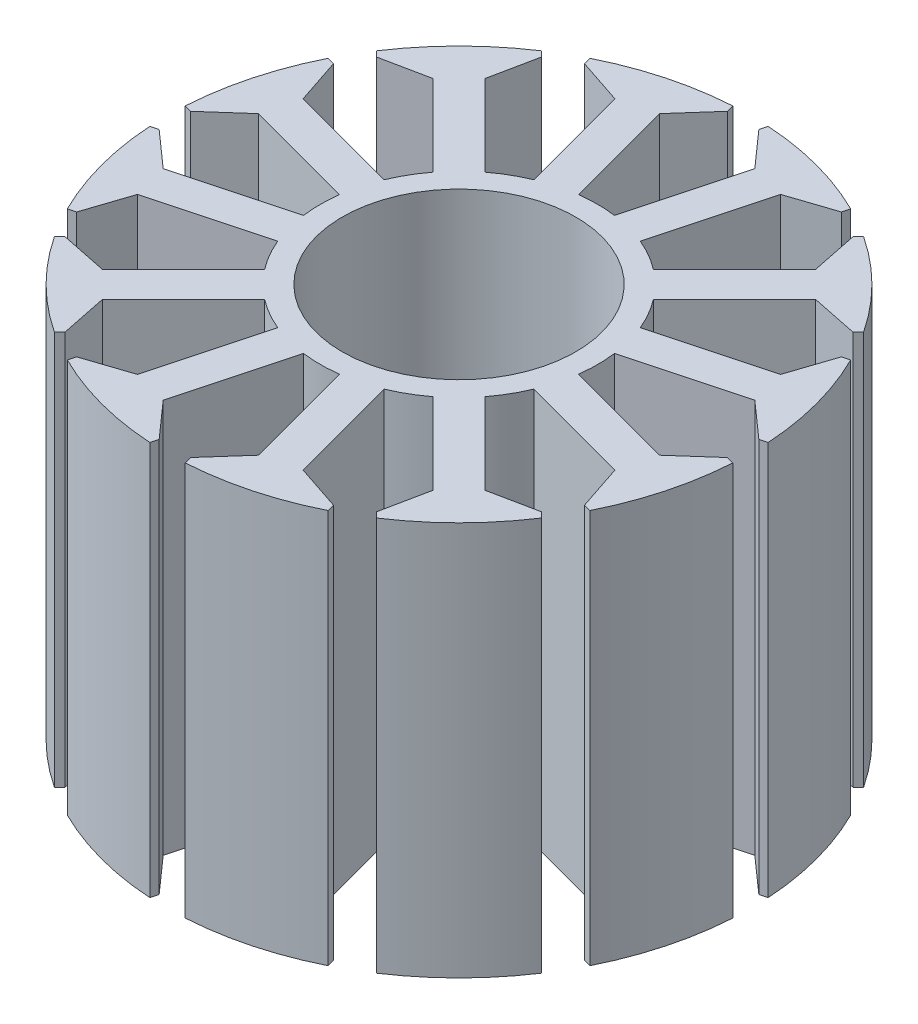
SolidWorks part; units mm, degrees
material "Ductile Iron"
ref_plane "Front Plane" through (0, 0, 0) normal (0, 0, 1) x (1, 0, 0)
ref_plane "Top Plane" through (0, 0, 0) normal (0, 1, 0) x (1, 0, 0)
ref_plane "Right Plane" through (0, 0, 0) normal (1, 0, 0) x (0, 0, -1)
sketch "Sketch1" plane through (0, 0, 0) normal (0, 1, 0) x (1, 0, 0)
  line L1 (0, 0) -> (0, 9.5) construction
  line L2 (0, 0) -> (10, 17.3205) construction
  line L3 (2.0706, 7.7274) -> (5.1764, 19.3185) construction
  line L4 (1.23, 9.42) -> (3.261, 17)
  line L5 (3.6448, 8.773) -> (5.6759, 16.353)
  line L6 (1.0755, 19.4634) -> (3.261, 17)
  line L7 (8.8003, 17.3935) -> (5.6759, 16.353)
  line L8 (16.3181, 10.6631) -> (13.0919, 11.3241)
  line L9 (8.8003, 17.3935) -> (8.9343, 17.8935)
  line L10 (1.0755, 19.4634) -> (1.2094, 19.9634)
  line L11 (16.3181, 10.6631) -> (16.6841, 11.0291)
  line L12 (10.6631, 16.3181) -> (11.0291, 16.6841)
  line L13 (10.6631, 16.3181) -> (11.3241, 13.0919)
  line L14 (5.7752, 7.543) -> (11.3241, 13.0919)
  line L15 (7.543, 5.7752) -> (13.0919, 11.3241)
  line L16 (19.4634, 1.0755) -> (17, 3.261)
  line L17 (19.4634, 1.0755) -> (19.9634, 1.2094)
  line L18 (17.3935, 8.8003) -> (17.8935, 8.9343)
  line L19 (17.3935, 8.8003) -> (16.353, 5.6759)
  line L20 (8.773, 3.6448) -> (16.353, 5.6759)
  line L21 (9.42, 1.23) -> (17, 3.261)
  line L22 (17.3935, -8.8003) -> (16.353, -5.6759)
  line L23 (17.3935, -8.8003) -> (17.8935, -8.9343)
  line L24 (19.4634, -1.0755) -> (19.9634, -1.2094)
  line L25 (19.4634, -1.0755) -> (17, -3.261)
  line L26 (9.42, -1.23) -> (17, -3.261)
  line L27 (8.773, -3.6448) -> (16.353, -5.6759)
  line L28 (10.6631, -16.3181) -> (11.3241, -13.0919)
  line L29 (10.6631, -16.3181) -> (11.0291, -16.6841)
  line L30 (16.3181, -10.6631) -> (16.6841, -11.0291)
  line L31 (16.3181, -10.6631) -> (13.0919, -11.3241)
  line L32 (7.543, -5.7752) -> (13.0919, -11.3241)
  line L33 (5.7752, -7.543) -> (11.3241, -13.0919)
  line L34 (1.0755, -19.4634) -> (3.261, -17)
  line L35 (1.0755, -19.4634) -> (1.2094, -19.9634)
  line L36 (8.8003, -17.3935) -> (8.9343, -17.8935)
  line L37 (8.8003, -17.3935) -> (5.6759, -16.353)
  line L38 (3.6448, -8.773) -> (5.6759, -16.353)
  line L39 (1.23, -9.42) -> (3.261, -17)
  line L40 (-8.8003, -17.3935) -> (-5.6759, -16.353)
  line L41 (-8.8003, -17.3935) -> (-8.9343, -17.8935)
  line L42 (-1.0755, -19.4634) -> (-1.2094, -19.9634)
  line L43 (-1.0755, -19.4634) -> (-3.261, -17)
  line L44 (-1.23, -9.42) -> (-3.261, -17)
  line L45 (-3.6448, -8.773) -> (-5.6759, -16.353)
  line L46 (-16.3181, -10.6631) -> (-13.0919, -11.3241)
  line L47 (-16.3181, -10.6631) -> (-16.6841, -11.0291)
  line L48 (-10.6631, -16.3181) -> (-11.0291, -16.6841)
  line L49 (-10.6631, -16.3181) -> (-11.3241, -13.0919)
  line L50 (-5.7752, -7.543) -> (-11.3241, -13.0919)
  line L51 (-7.543, -5.7752) -> (-13.0919, -11.3241)
  line L52 (-19.4634, -1.0755) -> (-17, -3.261)
  line L53 (-19.4634, -1.0755) -> (-19.9634, -1.2094)
  line L54 (-17.3935, -8.8003) -> (-17.8935, -8.9343)
  line L55 (-17.3935, -8.8003) -> (-16.353, -5.6759)
  line L56 (-8.773, -3.6448) -> (-16.353, -5.6759)
  line L57 (-9.42, -1.23) -> (-17, -3.261)
  line L58 (-17.3935, 8.8003) -> (-16.353, 5.6759)
  line L59 (-17.3935, 8.8003) -> (-17.8935, 8.9343)
  line L60 (-19.4634, 1.0755) -> (-19.9634, 1.2094)
  line L61 (-19.4634, 1.0755) -> (-17, 3.261)
  line L62 (-9.42, 1.23) -> (-17, 3.261)
  line L63 (-8.773, 3.6448) -> (-16.353, 5.6759)
  line L64 (-10.6631, 16.3181) -> (-11.3241, 13.0919)
  line L65 (-10.6631, 16.3181) -> (-11.0291, 16.6841)
  line L66 (-16.3181, 10.6631) -> (-16.6841, 11.0291)
  line L67 (-16.3181, 10.6631) -> (-13.0919, 11.3241)
  line L68 (-7.543, 5.7752) -> (-13.0919, 11.3241)
  line L69 (-5.7752, 7.543) -> (-11.3241, 13.0919)
  line L70 (-1.0755, 19.4634) -> (-3.261, 17)
  line L71 (-1.0755, 19.4634) -> (-1.2094, 19.9634)
  line L72 (-8.8003, 17.3935) -> (-8.9343, 17.8935)
  line L73 (-8.8003, 17.3935) -> (-5.6759, 16.353)
  line L74 (-3.6448, 8.773) -> (-5.6759, 16.353)
  line L75 (-1.23, 9.42) -> (-3.261, 17)
  arc A0 (8.9343, 17.8935) -> (1.2094, 19.9634) centre (0, 0) ccw
  arc A1 (4, 6.9282) -> (0, 8) centre (0, 0) ccw
  arc A2 (0, 9.5) -> (1.23, 9.42) centre (0, 0) cw
  arc A3 (3.6448, 8.773) -> (4.75, 8.2272) centre (0, 0) cw
  arc A4 (16.6841, 11.0291) -> (11.0291, 16.6841) centre (0, 0) ccw
  arc A5 (4.75, 8.2272) -> (5.7752, 7.543) centre (0, 0) cw
  arc A6 (7.543, 5.7752) -> (8.2272, 4.75) centre (0, 0) cw
  arc A7 (6.9282, 4) -> (4, 6.9282) centre (0, 0) ccw
  arc A8 (19.9634, 1.2094) -> (17.8935, 8.9343) centre (0, 0) ccw
  arc A9 (8.2272, 4.75) -> (8.773, 3.6448) centre (0, 0) cw
  arc A10 (9.42, 1.23) -> (9.5, 0) centre (0, 0) cw
  arc A11 (8, 0) -> (6.9282, 4) centre (0, 0) ccw
  arc A12 (17.8935, -8.9343) -> (19.9634, -1.2094) centre (0, 0) ccw
  arc A13 (9.5, 0) -> (9.42, -1.23) centre (0, 0) cw
  arc A14 (8.773, -3.6448) -> (8.2272, -4.75) centre (0, 0) cw
  arc A15 (6.9282, -4) -> (8, 0) centre (0, 0) ccw
  arc A16 (11.0291, -16.6841) -> (16.6841, -11.0291) centre (0, 0) ccw
  arc A17 (8.2272, -4.75) -> (7.543, -5.7752) centre (0, 0) cw
  arc A18 (5.7752, -7.543) -> (4.75, -8.2272) centre (0, 0) cw
  arc A19 (4, -6.9282) -> (6.9282, -4) centre (0, 0) ccw
  arc A20 (1.2094, -19.9634) -> (8.9343, -17.8935) centre (0, 0) ccw
  arc A21 (4.75, -8.2272) -> (3.6448, -8.773) centre (0, 0) cw
  arc A22 (1.23, -9.42) -> (0, -9.5) centre (0, 0) cw
  arc A23 (0, -8) -> (4, -6.9282) centre (0, 0) ccw
  arc A24 (-8.9343, -17.8935) -> (-1.2094, -19.9634) centre (0, 0) ccw
  arc A25 (0, -9.5) -> (-1.23, -9.42) centre (0, 0) cw
  arc A26 (-3.6448, -8.773) -> (-4.75, -8.2272) centre (0, 0) cw
  arc A27 (-4, -6.9282) -> (0, -8) centre (0, 0) ccw
  arc A28 (-16.6841, -11.0291) -> (-11.0291, -16.6841) centre (0, 0) ccw
  arc A29 (-4.75, -8.2272) -> (-5.7752, -7.543) centre (0, 0) cw
  arc A30 (-7.543, -5.7752) -> (-8.2272, -4.75) centre (0, 0) cw
  arc A31 (-6.9282, -4) -> (-4, -6.9282) centre (0, 0) ccw
  arc A32 (-19.9634, -1.2094) -> (-17.8935, -8.9343) centre (0, 0) ccw
  arc A33 (-8.2272, -4.75) -> (-8.773, -3.6448) centre (0, 0) cw
  arc A34 (-9.42, -1.23) -> (-9.5, 0) centre (0, 0) cw
  arc A35 (-8, 0) -> (-6.9282, -4) centre (0, 0) ccw
  arc A36 (-17.8935, 8.9343) -> (-19.9634, 1.2094) centre (0, 0) ccw
  arc A37 (-9.5, 0) -> (-9.42, 1.23) centre (0, 0) cw
  arc A38 (-8.773, 3.6448) -> (-8.2272, 4.75) centre (0, 0) cw
  arc A39 (-6.9282, 4) -> (-8, 0) centre (0, 0) ccw
  arc A40 (-11.0291, 16.6841) -> (-16.6841, 11.0291) centre (0, 0) ccw
  arc A41 (-8.2272, 4.75) -> (-7.543, 5.7752) centre (0, 0) cw
  arc A42 (-5.7752, 7.543) -> (-4.75, 8.2272) centre (0, 0) cw
  arc A43 (-4, 6.9282) -> (-6.9282, 4) centre (0, 0) ccw
  arc A44 (-1.2094, 19.9634) -> (-8.9343, 17.8935) centre (0, 0) ccw
  arc A45 (-4.75, 8.2272) -> (-3.6448, 8.773) centre (0, 0) cw
  arc A46 (-1.23, 9.42) -> (0, 9.5) centre (0, 0) cw
  arc A47 (0, 8) -> (-4, 6.9282) centre (0, 0) ccw
  point P152 (0, 0)
  dimension "D1" = 8
  dimension "D2" = 20
  dimension "D4" = 9.5
  dimension "D6" = 0.5
  dimension "D3" = 30
  dimension "D5" = 2.5
  dimension "D7" = 3
  dimension "D8" = 12
extrude "Boss-Extrude1" add sketch "Sketch1" along normal blind 27 contours A46 L75 L70 L71 A44 L72 L73 L74 A45 A42 L69 L64 L65 A40 L66 L67 L68 A41 A38 L63 L58 L59 A36 L60 L61 L62 A37 A34 L57 L52 L53 A32 L54 L55 L56 A33 A30 L51 L46 L47 A28 L48 L49 L50 A29 A26 L45 L40 L41 A24 L42
